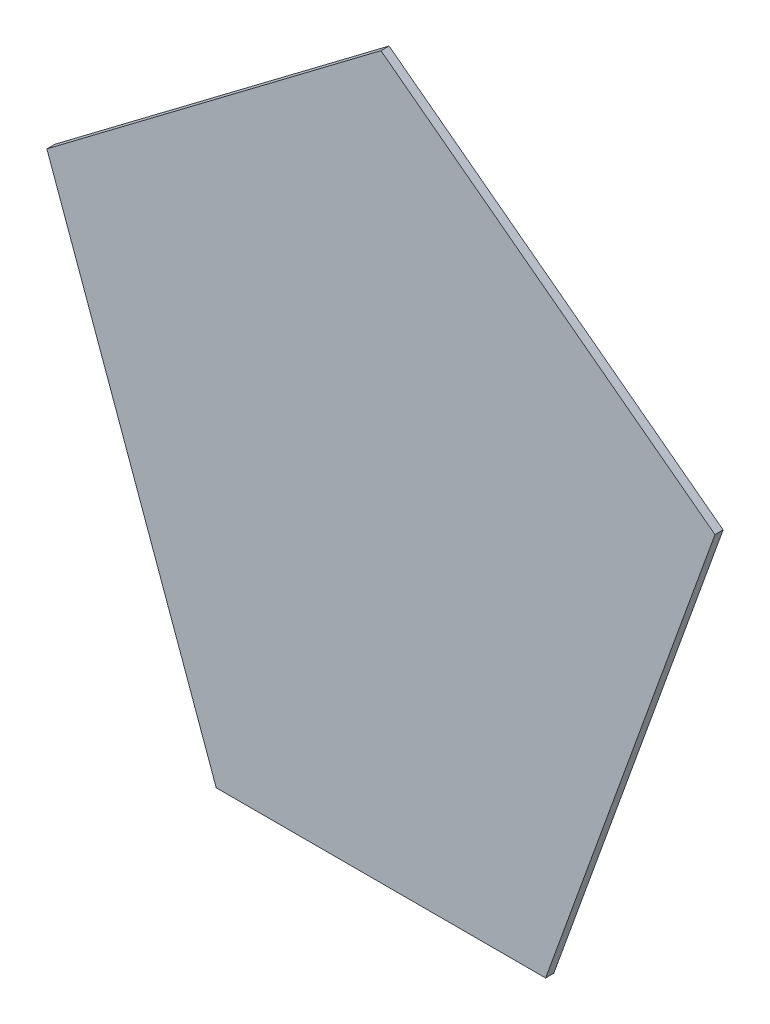
SolidWorks part; units mm, degrees
ref_plane "Plan de face" through (0, 0, 0) normal (0, 0, 1) x (1, 0, 0)
ref_plane "Plan de dessus" through (0, 0, 0) normal (0, 1, 0) x (1, 0, 0)
ref_plane "Plan de droite" through (0, 0, 0) normal (1, 0, 0) x (0, 0, -1)
sketch "Esquisse1" plane through (0, 0, 0) normal (0, 0, 1) x (1, 0, 0)
  line L0 (-7.7725, -270.0266) -> (-151.4599, -378.4422)
  line L1 (-151.4599, -378.4422) -> (-78.6086, -580.0266)
  line L2 (-78.6086, -580.0266) -> (63.0636, -580.0266)
  line L3 (-7.7725, -580.0266) -> (-7.7725, -270.0266) construction
  line L6 (-7.7725, -270.0266) -> (135.9149, -378.4422)
  line L7 (135.9149, -378.4422) -> (63.0636, -580.0266)
  dimension "D1" = 310
extrude "Boss.-Extru.1" add sketch "Esquisse1" against normal blind 3.5
